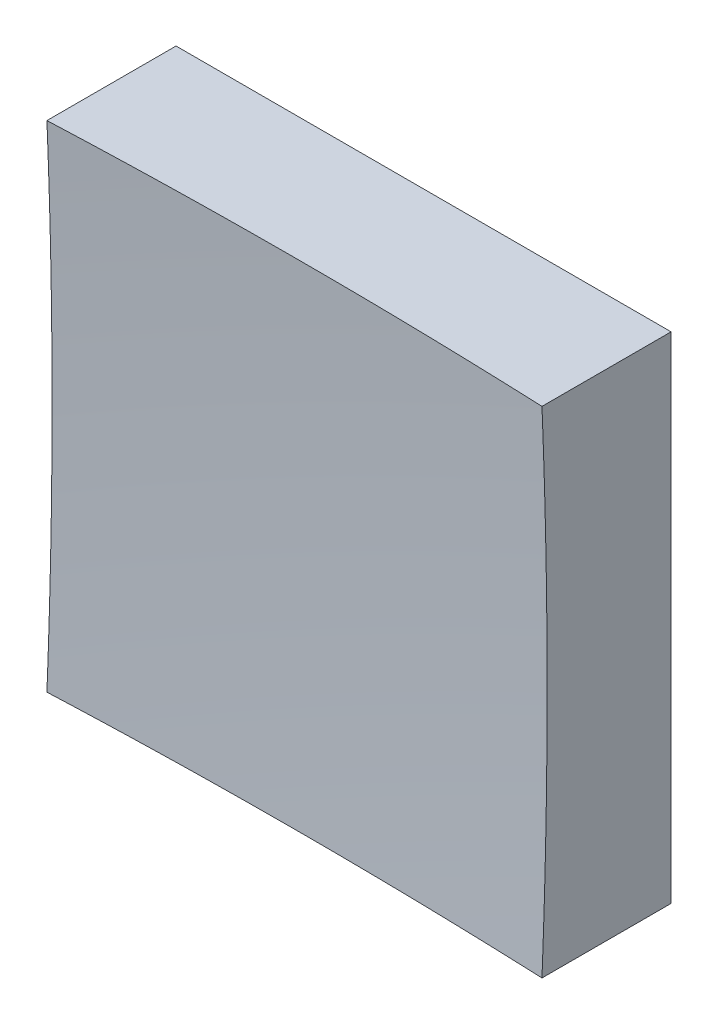
SolidWorks part; units mm, degrees
ref_plane "前视基准面" through (0, 0, 0) normal (0, 0, 1) x (1, 0, 0)
ref_plane "上视基准面" through (0, 0, 0) normal (0, 1, 0) x (1, 0, 0)
ref_plane "右视基准面" through (0, 0, 0) normal (1, 0, 0) x (0, 0, -1)
sketch "草图1" plane through (0, 0, 0) normal (0, 0, 1) x (1, 0, 0)
  line L1 (-6.25, 6.25) -> (6.25, 6.25)
  line L2 (-6.25, 6.25) -> (-6.25, -6.25)
  line L3 (-6.25, -6.25) -> (6.25, -6.25)
  line L4 (6.25, 6.25) -> (6.25, -6.25)
  line L5 (-6.25, 6.25) -> (6.25, -6.25) construction
  line L6 (-6.25, -6.25) -> (6.25, 6.25) construction
  point P0 (0, 0)
  dimension "D1" = 12.5
  dimension "D2" = 12.5
extrude "凸台-拉伸1" add sketch "草图1" along normal blind 10 contours L2 L3 L4 L1
sketch "草图2" plane through (0, 0, 0) normal (0, 1, 0) x (1, 0, 0)
  line L0 (-7.4603, -3) -> (7.3192, -3) construction
  line L1 (0, 0) -> (0, -12.1749) construction
  line L2 (146.2268, -119.5677) -> (0, -119.5677)
  line L3 (0, -119.5677) -> (0, -3)
  arc A1 (146.2268, -119.5677) -> (0, -3) centre (0, -153) ccw
  dimension "D2" = 300
  dimension "D1" = 3
revolve "切除-旋转2" cut sketch "草图2" angle 360 about L3
